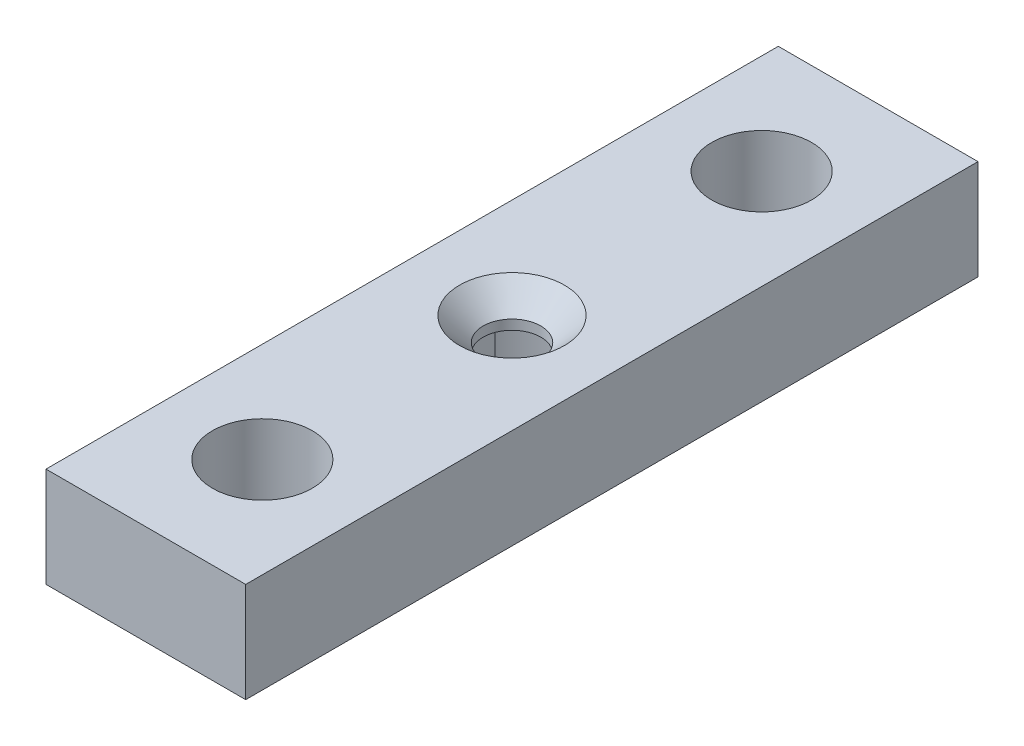
SolidWorks part; units mm, degrees
material "Alum 6061 (Default)"
ref_plane "Front Plane" through (0, 0, 0) normal (0, 0, 1) x (1, 0, 0)
ref_plane "Top Plane" through (0, 0, 0) normal (0, 1, 0) x (1, 0, 0)
ref_plane "Right Plane" through (0, 0, 0) normal (1, 0, 0) x (0, 0, -1)
sketch "Sketch1" plane through (0, 0, 0) normal (0, 0, 1) x (1, 0, 0)
  line L1 (-19.05, 9.525) -> (19.05, 9.525)
  line L2 (-19.05, 9.525) -> (-19.05, -9.525)
  line L3 (-19.05, -9.525) -> (19.05, -9.525)
  line L4 (19.05, 9.525) -> (19.05, -9.525)
  line L5 (-19.05, 9.525) -> (19.05, -9.525) construction
  line L6 (-19.05, -9.525) -> (19.05, 9.525) construction
  point P0 (0, 0)
  dimension "Width" = 38.1
  dimension "Height" = 19.05
extrude "Extrude1" add sketch "Sketch1" along normal mid plane 139.7
sketch "Sketch2" plane through (0, 9.525, 0) normal (0, 1, 0) x (1, 0, 0)
  line L0 (0, 47.625) -> (0, -47.625) construction
  circle A0 centre (0, 47.625) radius 9.525
  circle A1 centre (0, -47.625) radius 9.525
  point P4 (0, 0)
  dimension "D2" = 19.05
  dimension "D1" = 95.25
extrude "Cut-Extrude1" cut sketch "Sketch2" against normal up to next
hole_wizard "CSK for M10 Flat Head Machine Screw1" positions "Sketch3" profile "Sketch4" countersink size "M10" standard "ANSI Metric"
sketch "Sketch3" plane through (0, 9.525, 0) normal (0, 1, 0) x (-1, 0, 0)
  point P0 (0, 0)
sketch "Sketch4" plane through (0, 9.525, 0) normal (1, 0, 0) x (0, 0, 1)
  line L0 (0, 0) -> (0, 32.7687)
  line L1 (0, 32.7687) -> (5.5, 29.464)
  line L2 (5.5, 29.464) -> (5.5, 4.5)
  line L3 (5.5, 4.5) -> (10, 0)
  line L5 (10, 0) -> (0, 0)
  line L6 (-5.5, 4.5) -> (-10, 0) construction
  line L10 (0, 32.7687) -> (-5.5, 29.464) construction
  line L11 (0, -6.35) -> (0, 107.95) construction
  dimension "Hole Dia." = 11
  dimension "Hole Depth" = 29.464
  dimension "Near C'Sink Dia." = 20
  dimension "Near C'Sink Angle" = 90
  dimension "Drill Angle" = 118
sketch "Sketch5" plane through (0, -9.525, 0) normal (0, -1, 0) x (1, 0, 0)
  circle A2 centre (0, 0) radius 15.9385
  dimension "D1" = 31.877
extrude "Cut-Extrude2" cut sketch "Sketch5" against normal blind 12.7
sketch "Sketch6" plane through (0, -9.525, 0) normal (0, -1, 0) x (1, 0, 0)
  line L10 (-12.7635, 9.5461) -> (-12.7635, -9.5461)
  line L12 (12.7635, 9.5461) -> (12.7635, -9.5461)
  circle A6 centre (0, 0) radius 15.9385 construction
  arc A7 (-12.7635, 9.5461) -> (-12.7635, -9.5461) centre (0, 0) ccw
  arc A8 (12.7635, -9.5461) -> (12.7635, 9.5461) centre (0, 0) ccw
  point P0 (0, 0)
  dimension "D1" = 25.527
extrude "Boss-Extrude1" add sketch "Sketch6" against normal up to surface (12.7 mm away) up to face at (0, 3.175, -15.9385)
